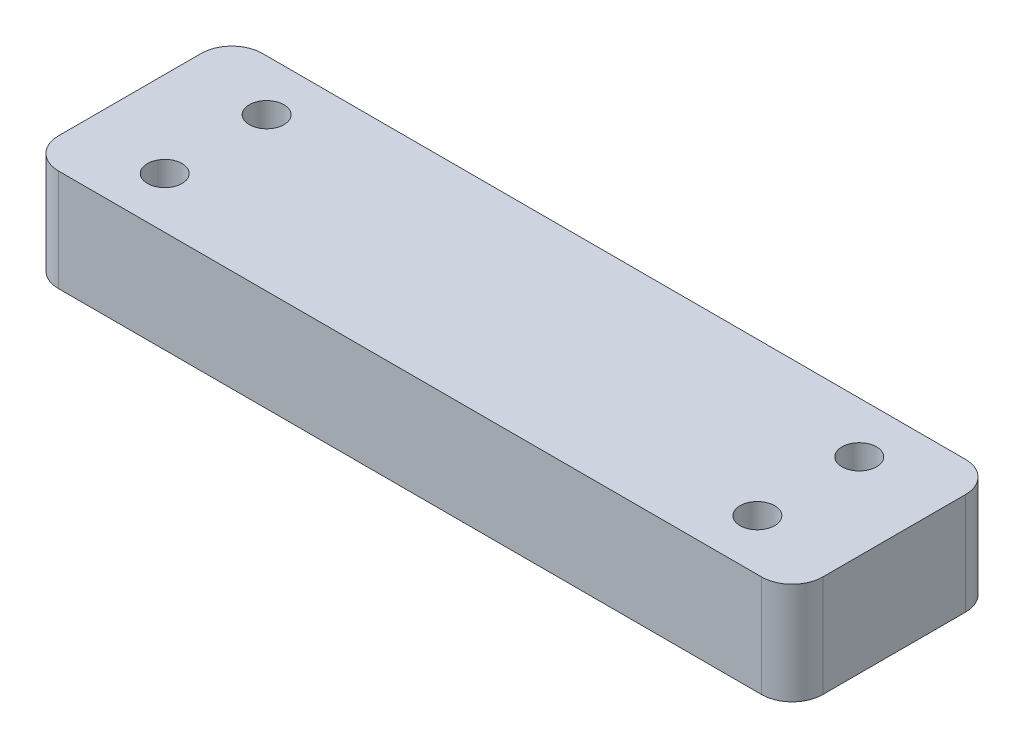
SolidWorks part; units mm, degrees
ref_plane "Front Plane" through (0, 0, 0) normal (0, 0, 1) x (1, 0, 0)
ref_plane "Top Plane" through (0, 0, 0) normal (0, 1, 0) x (1, 0, 0)
ref_plane "Right Plane" through (0, 0, 0) normal (1, 0, 0) x (0, 0, -1)
sketch "Sketch1" plane through (0, 0, 0) normal (0, 1, 0) x (1, 0, 0)
  line L1 (0, 0) -> (75, 0)
  line L2 (0, 0) -> (0, 20)
  line L3 (0, 20) -> (75, 20)
  line L4 (75, 0) -> (75, 20)
  dimension "D1" = 75
  dimension "D2" = 20
extrude "Boss-Extrude1" add sketch "Sketch1" along normal blind 10
fillet "Fillet1" radius 3 4 edges at (0, 5, -20) (0, 5, 0) (75, 5, -20) (75, 5, 0)
hole_wizard "M3 Clearance Hole1" positions "Sketch2" profile "Sketch3" hole size "M3" standard "ANSI Metric" end condition through all
sketch "Sketch2" plane through (67.5353, 10, -35.4163) normal (0, 1, 0) x (1, 0, 0)
  point P0 (-0.9543, -20.4163)
  point P1 (-0.9543, -30.4163)
  point P4 (-59.1163, -30.4163)
  point P5 (-59.1163, -20.4163)
sketch "Sketch3" plane through (66.581, 10, -15) normal (1, 0, 0) x (0, 0, 1)
  line L0 (0, 0) -> (0, 10)
  line L1 (0, 10) -> (1.7, 10)
  line L2 (1.7, 10) -> (1.7, 0)
  line L3 (1.7, 0) -> (0, 0)
  line L4 (0, -6.35) -> (0, 107.95) construction
  dimension "Thru Hole Dia." = 3.4
  dimension "Thru Hole Depth" = 10
